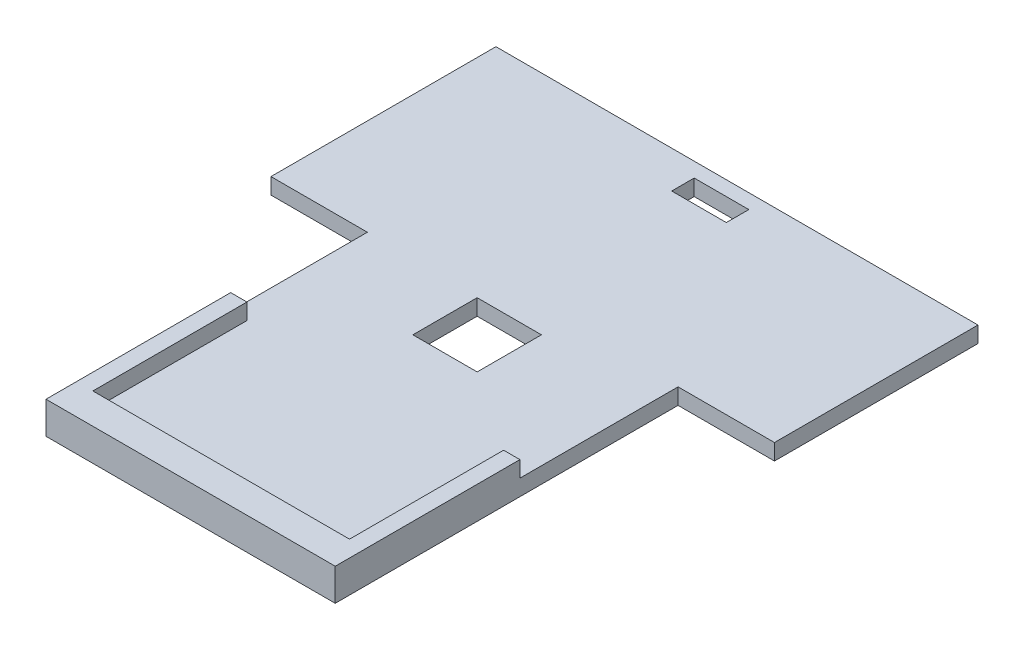
SolidWorks part; units mm, degrees
ref_plane "Front Plane" through (0, 0, 0) normal (0, 0, 1) x (1, 0, 0)
ref_plane "Top Plane" through (0, 0, 0) normal (0, 1, 0) x (1, 0, 0)
ref_plane "Right Plane" through (0, 0, 0) normal (1, 0, 0) x (0, 0, -1)
sketch "Sketch2" plane through (0, 0, 0) normal (0, 1, 0) x (1, 0, 0)
  line L0 (0.021, 80.5643) -> (0.021, 72.5143) construction
  line L1 (-44.719, -89.4357) -> (45.281, -89.4357)
  line L2 (-74.719, 10.5643) -> (-74.719, 80.5643)
  line L3 (-74.719, 80.5643) -> (75.281, 80.5643)
  line L4 (75.281, 17.2355) -> (75.281, 80.5643)
  line L5 (-44.719, -55.4357) -> (75.281, 80.5643) construction
  line L6 (-74.719, 80.5643) -> (45.281, -48.7645) construction
  line L7 (-74.719, 10.5643) -> (-44.719, 10.5643)
  line L8 (-44.719, 10.5643) -> (-44.719, -89.4357)
  line L9 (75.281, 17.2355) -> (45.281, 17.2355)
  line L10 (45.281, 17.2355) -> (45.281, -89.4357)
  line L11 (0.021, 72.5143) -> (75.281, 72.5143) construction
  line L13 (-8.479, 69.0143) -> (8.521, 69.0143)
  line L14 (-8.479, 69.0143) -> (-8.479, 76.0143)
  line L15 (-8.479, 76.0143) -> (8.521, 76.0143)
  line L16 (8.521, 69.0143) -> (8.521, 76.0143)
  line L17 (-8.479, 69.0143) -> (8.521, 76.0143) construction
  line L18 (-8.479, 76.0143) -> (8.521, 69.0143) construction
  point P0 (2.1668, -2.2986)
  dimension "D4" = 75.26
  dimension "D5" = 8.05
  dimension "D1" = 150
  dimension "D2" = 30
  dimension "D3" = 30
  dimension "D6" = 17
  dimension "D7" = 7
extrude "Boss-Extrude1" add sketch "Sketch2" along normal blind 5
sketch "Sketch3" plane through (0, 5, 0) normal (0, 1, 0) x (1, 0, 0)
  line L0 (0.281, -89.4357) -> (0, 0) construction
  line L1 (-44.719, -89.4357) -> (45.281, -89.4357) construction
  line L3 (-10, -10) -> (10, -10)
  line L4 (-10, -10) -> (-10, 10)
  line L5 (-10, 10) -> (10, 10)
  line L6 (10, -10) -> (10, 10)
  line L7 (-10, -10) -> (10, 10) construction
  line L8 (-10, 10) -> (10, -10) construction
  dimension "D1" = 89.4357
  dimension "D2" = 20
  dimension "D3" = 20
extrude "Cut-Extrude1" cut sketch "Sketch3" against normal blind 5
ref_plane "Plane1" through (-74.719, 0, -80.5643) normal (0, 0, 1) x (1, 0, 0)
sketch "Sketch5" plane through (0, 5, 0) normal (0, 1, 0) x (1, 0, 0)
  line L1 (-39.6505, -79.9218) -> (40.2126, -79.9218)
  line L2 (-44.719, -79.9218) -> (-44.719, -89.4357)
  line L3 (-44.719, -89.4357) -> (45.281, -89.4357)
  line L4 (45.281, -79.9218) -> (45.281, -89.4357)
  line L5 (0.281, -84.6788) -> (45.281, -89.4357) construction
  line L6 (-44.719, -89.4357) -> (0.281, -84.6788) construction
  line L7 (40.2126, -31.9752) -> (45.281, -31.9752)
  line L8 (40.2126, -31.9752) -> (40.2126, -79.9218)
  line L10 (45.281, -31.9752) -> (45.281, -79.9218)
  line L11 (40.2126, -31.9752) -> (45.281, -79.9218) construction
  line L12 (40.2126, -79.9218) -> (45.281, -31.9752) construction
  line L13 (-39.6505, -31.9752) -> (-44.719, -31.9752)
  line L14 (-39.6505, -31.9752) -> (-39.6505, -79.9218)
  line L16 (-44.719, -31.9752) -> (-44.719, -79.9218)
  line L17 (-39.6505, -31.9752) -> (-44.719, -79.9218) construction
  line L18 (-39.6505, -79.9218) -> (-44.719, -31.9752) construction
  point P0 (0.281, -84.6788)
  point P6 (42.7468, -55.9485)
  point P7 (-42.1848, -55.9485)
extrude "Boss-Extrude2" add sketch "Sketch5" along normal blind 5
